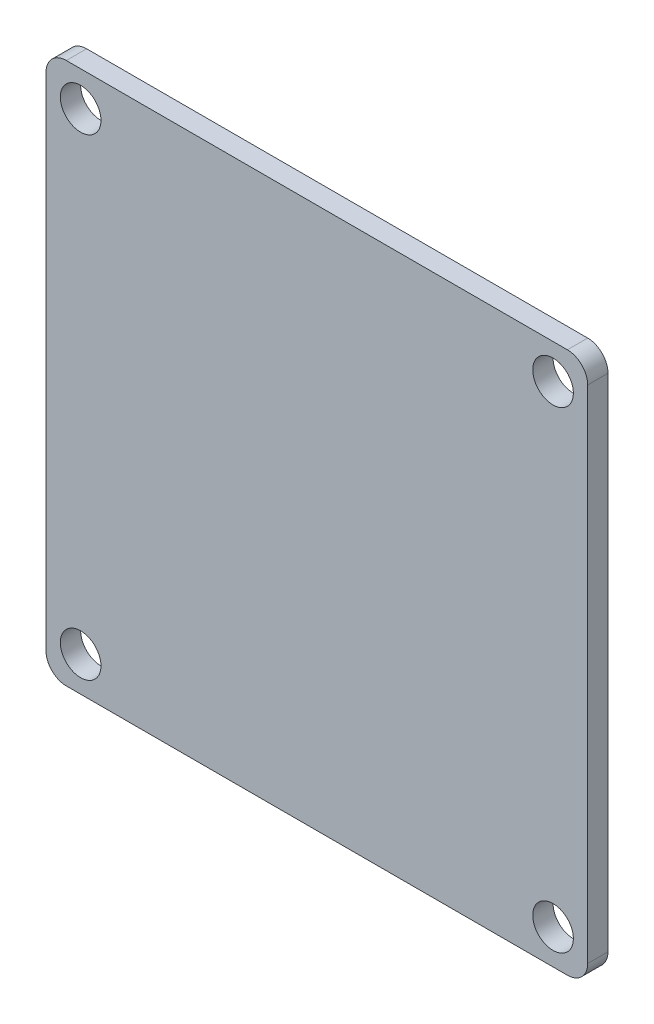
SolidWorks part; units mm, degrees
ref_plane "前视基准面" through (0, 0, 0) normal (0, 0, 1) x (1, 0, 0)
ref_plane "上视基准面" through (0, 0, 0) normal (0, 1, 0) x (1, 0, 0)
ref_plane "右视基准面" through (0, 0, 0) normal (1, 0, 0) x (0, 0, -1)
sketch "草图1" plane through (0, 0, 0) normal (0, 0, 1) x (1, 0, 0)
  line L1 (-18.5, -20) -> (18.5, -20)
  line L2 (-20, -18.5) -> (-20, 18.5)
  line L3 (-18.5, 20) -> (18.5, 20)
  line L4 (20, -18.5) -> (20, 18.5)
  circle A2 centre (-17.4424, 17.4424) radius 1.5
  circle A3 centre (17.4424, 17.4424) radius 1.5
  circle A4 centre (17.4424, -17.4424) radius 1.5
  circle A5 centre (-17.4424, -17.4424) radius 1.5
  arc A6 (-18.5, -20) -> (-20, -18.5) centre (-18.5, -18.5) cw
  arc A7 (18.5, -20) -> (20, -18.5) centre (18.5, -18.5) ccw
  arc A8 (20, 18.5) -> (18.5, 20) centre (18.5, 18.5) ccw
  arc A9 (-20, 18.5) -> (-18.5, 20) centre (-18.5, 18.5) cw
  point P0 (0, 0)
  point P6 (0, 0)
  dimension "D7" = 3
  dimension "D9" = 1.5
  dimension "D8" = 4
extrude "凸台-拉伸1" add sketch "草图1" along normal blind 1.5
